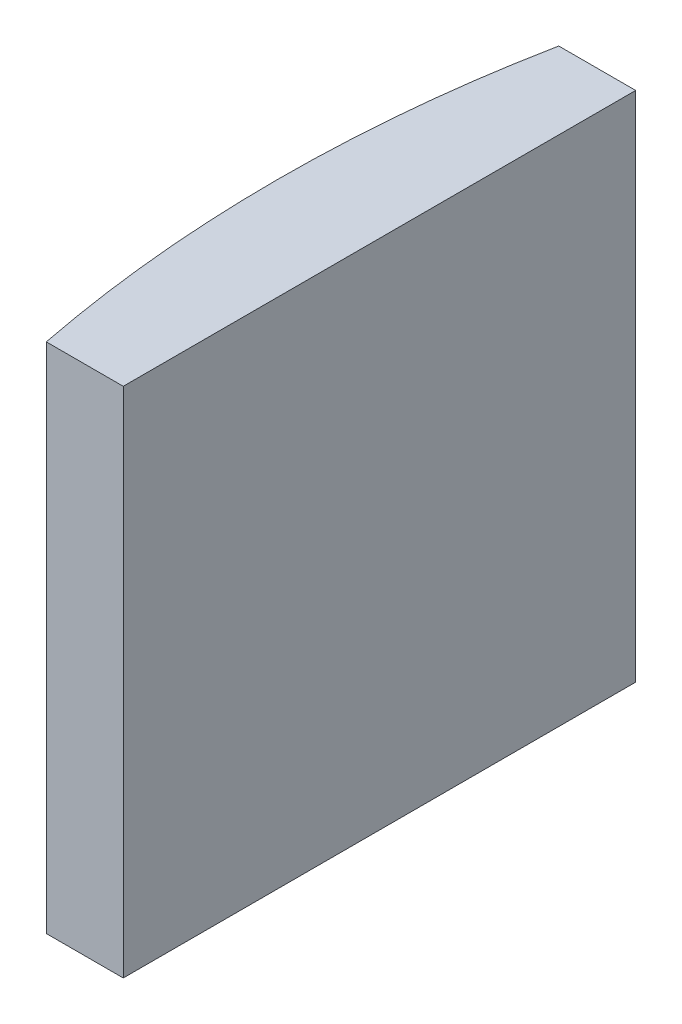
SolidWorks part; units mm, degrees
ref_plane "前视基准面" through (0, 0, 0) normal (0, 0, 1) x (1, 0, 0)
ref_plane "上视基准面" through (0, 0, 0) normal (0, 1, 0) x (1, 0, 0)
ref_plane "右视基准面" through (0, 0, 0) normal (1, 0, 0) x (0, 0, -1)
sketch "草图1" plane through (0, 0, 0) normal (0, 1, 0) x (1, 0, 0)
  line L0 (10.7432, 0) -> (-58.0207, 0) construction
  line L1 (-46.3481, 10) -> (-43.3448, 10)
  line L2 (-46.3481, -10) -> (-43.3448, -10)
  line L3 (-43.3448, 10) -> (-43.3448, -10)
  arc A0 (-46.3481, 10) -> (-46.3481, -10) centre (4.3552, 0) ccw
  point P2 (-58.0207, 0)
  point P19 (-47.3248, 0)
  point P20 (-43.3448, 0)
  dimension "D2" = 10
  dimension "D3" = 51.68
  dimension "D4" = 3.98
  dimension "D1" = 10
extrude "凸台-拉伸1" add sketch "草图1" along normal blind 20
